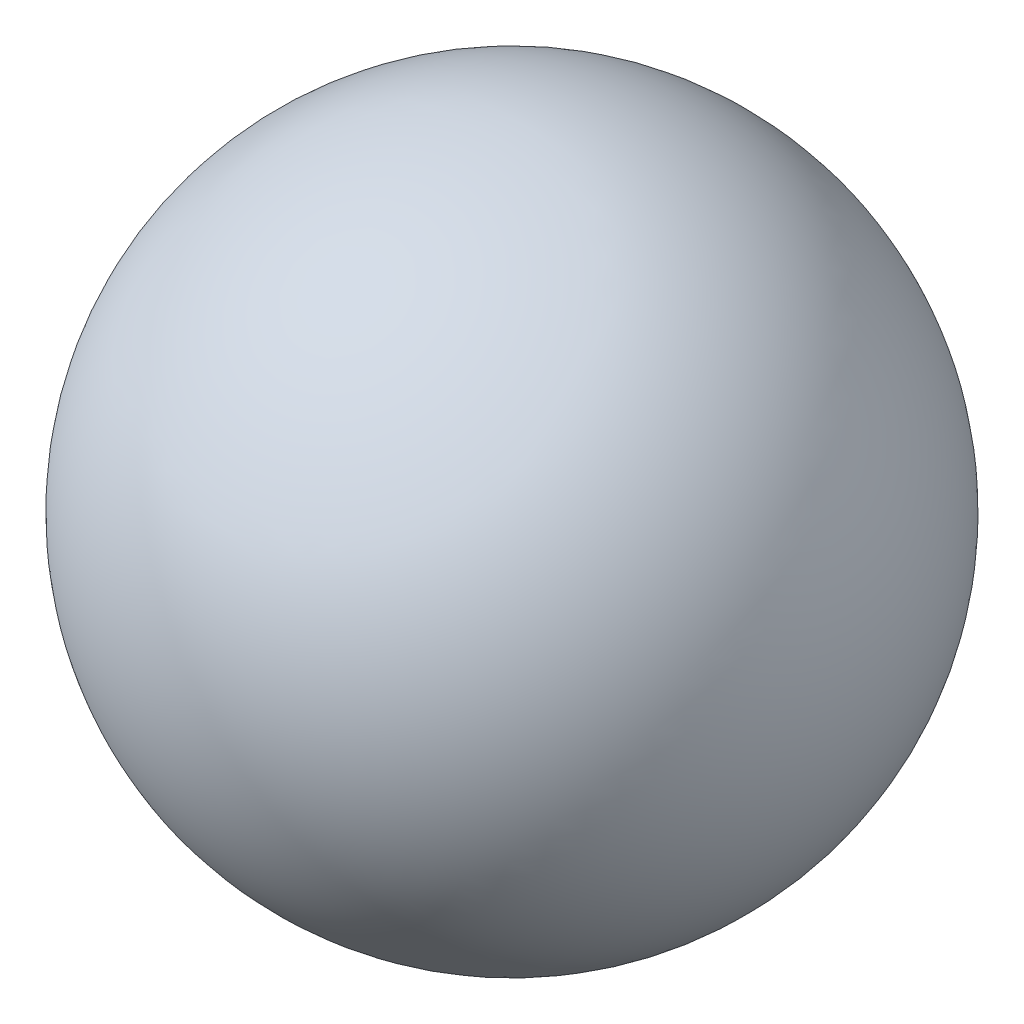
SolidWorks part; units mm, degrees
material "Легированная сталь"
ref_plane "Спереди" through (0, 0, 0) normal (0, 0, 1) x (1, 0, 0)
ref_plane "Сверху" through (0, 0, 0) normal (0, 1, 0) x (1, 0, 0)
ref_plane "Справа" through (0, 0, 0) normal (1, 0, 0) x (0, 0, -1)
sketch "Эскиз1" plane through (0, 0, 0) normal (1, 0, 0) x (0, 0, -1)
  line L0 (-1.625, 0) -> (1.625, 0)
  arc A0 (1.625, 0) -> (-1.625, 0) centre (0, 0) ccw
  dimension "D1" = 3.25
revolve "Повернуть1" add sketch "Эскиз1" angle 360 about L0
